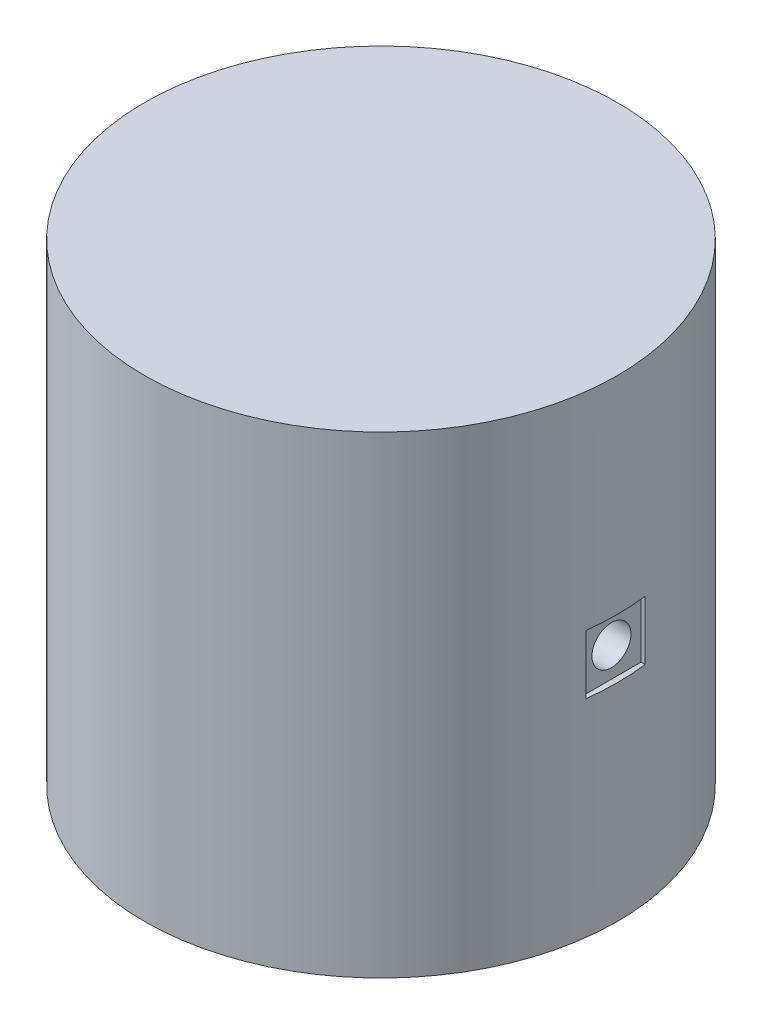
SolidWorks part; units mm, degrees
material "6061 Alloy"
ref_plane "Front Plane" through (0, 0, 0) normal (0, 0, 1) x (1, 0, 0)
ref_plane "Top Plane" through (0, 0, 0) normal (0, 1, 0) x (1, 0, 0)
ref_plane "Right Plane" through (0, 0, 0) normal (1, 0, 0) x (0, 0, -1)
sketch "Sketch1" plane through (0, 0, 0) normal (0, 1, 0) x (1, 0, 0)
  circle A0 centre (0, 0) radius 20
  dimension "D1" = 40
extrude "Boss-Extrude1" add sketch "Sketch1" along normal blind 40
sketch "Sketch2" plane through (0, 40, 0) normal (0, 1, 0) x (1, 0, 0)
  line L0 (0, 0) -> (0, 20) construction
  line L1 (0, 0) -> (20, 0) construction
  circle A0 centre (0, 0) radius 20 construction
ref_plane "Plane1" through (0, 0, -20) normal (0, 0, -1) x (-1, 0, 0)
sketch "Sketch3" plane through (0, 0, -20) normal (0, 0, -1) x (-1, 0, 0)
  line L0 (0, 0) -> (0, 40) construction
  circle A0 centre (0, 20) radius 4
  dimension "D2" = 8
  dimension "D1" = 40
extrude "Cut-Extrude1" cut sketch "Sketch3" against normal blind 30
ref_plane "Plane2" through (20, 0, 0) normal (1, 0, 0) x (0, 0, -1)
sketch "Sketch4" plane through (20, 0, 0) normal (1, 0, 0) x (0, 0, -1)
  line L0 (-20, 20) -> (20, 20) construction
  line L1 (-20, 40) -> (-20, 0) construction
  line L2 (20, -22) -> (20, 22) construction
  line L3 (0, 0) -> (0, 40) construction
  line L5 (-2.5, 17.5) -> (2.5, 17.5)
  line L6 (-2.5, 17.5) -> (-2.5, 22.5)
  line L7 (-2.5, 22.5) -> (2.5, 22.5)
  line L8 (2.5, 17.5) -> (2.5, 22.5)
  line L9 (-2.5, 17.5) -> (2.5, 22.5) construction
  line L10 (-2.5, 22.5) -> (2.5, 17.5) construction
  point P8 (0, 20)
  point P10 (0, 20)
  dimension "D1" = 40
  dimension "D2" = 5
  dimension "D3" = 5
hole_wizard "M4x0.7 Tapped Hole1" positions "3DSketch8" profile "Sketch12" tap size "M4x0.7" standard "ANSI Metric"
sketch3d "3DSketch8"
  line L0 (20, 20, 20) -> (20, 20, -20) construction
  point P0 (20, 20, 0)
  dimension "D1" = 20
  dimension "D2" = 0
sketch "Sketch12" plane through (20, 20, 0) normal (0, 1, 0) x (0, 0, -1)
  line L0 (0, 0) -> (0, 16)
  line L1 (0, 16) -> (1.65, 16)
  line L2 (1.65, 16) -> (1.65, 0)
  line L5 (1.65, 0) -> (0, 0)
  line L11 (0, -6.35) -> (0, 107.95) construction
  dimension "Thru Tap Drill Dia." = 3.3
  dimension "Thru Tap Drill Depth" = 16
cosmetic thread "Hole Thread1" parameters "D2"=4
ref_plane "Plane3" through (0, 0, 20) normal (0, 0, 1) x (1, 0, 0)
sketch "Sketch13" plane through (0, 0, 20) normal (0, 0, 1) x (1, 0, 0)
  line L0 (0, 0) -> (0, 40) construction
  line L1 (20, 40) -> (-20, 40) construction
  line L2 (20, 20) -> (-20, 20) construction
  line L3 (-20, 40) -> (-20, 0) construction
  point P10 (0, 20)
extrude "Cut-Extrude2" cut sketch "Sketch4" against normal blind 0.5
